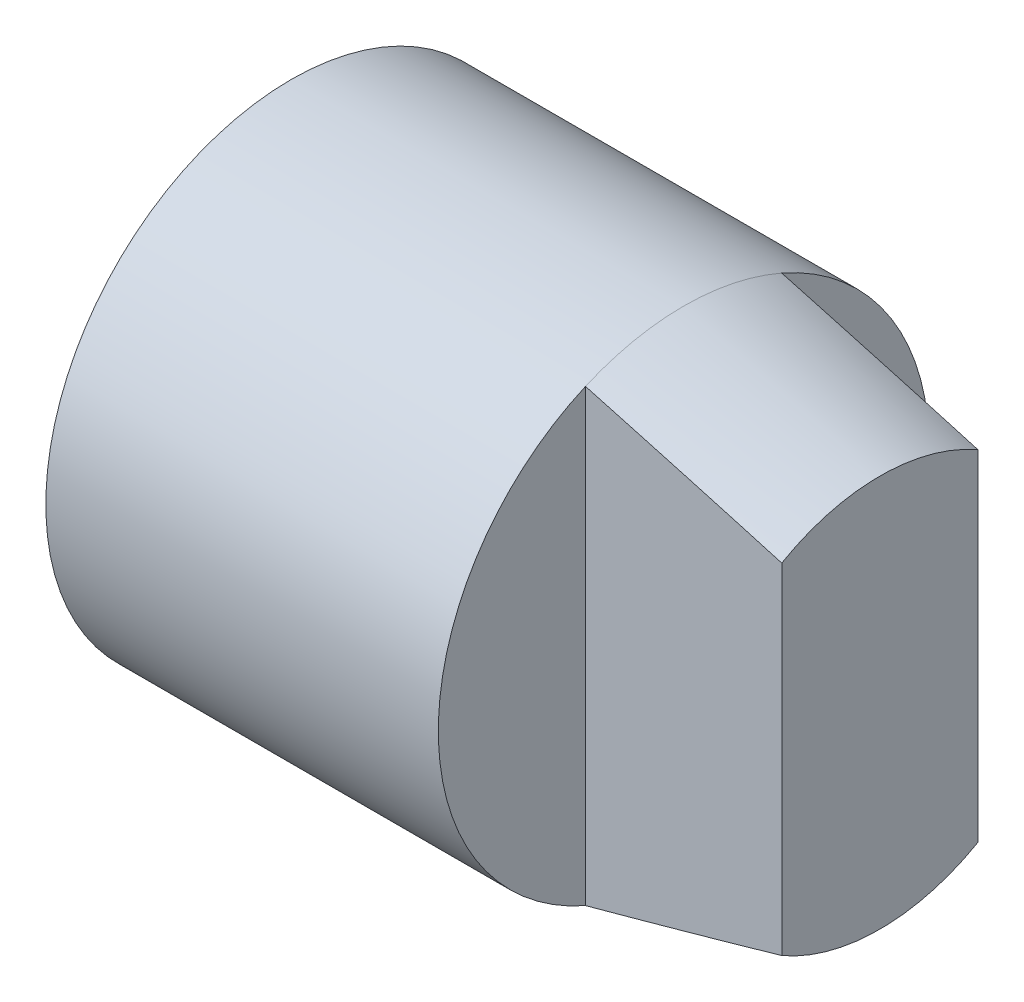
SolidWorks part; units mm, degrees
material "Plain Carbon Steel"
ref_plane "Front Plane" through (0, 0, 0) normal (0, 0, 1) x (1, 0, 0)
ref_plane "Top Plane" through (0, 0, 0) normal (0, 1, 0) x (1, 0, 0)
ref_plane "Right Plane" through (0, 0, 0) normal (1, 0, 0) x (0, 0, -1)
sketch "Sketch1" plane through (0, 0, 0) normal (0, 0, 1) x (1, 0, 0)
  line L0 (0, 0) -> (0, 5)
  line L1 (0, 5) -> (8, 5)
  line L2 (8, 5) -> (12, 4)
  line L3 (12, 4) -> (12, 0)
  line L4 (12, 0) -> (0, 0)
  dimension "D1" = 8
  dimension "D2" = 4
  dimension "D3" = 5
  dimension "D4" = 4
revolve "Revolve1" add sketch "Sketch1" angle 360 about L4
sketch "Sketch2" plane through (12, 0, 0) normal (1, 0, 0) x (0, 0, -1)
  line L0 (-2, 4.5826) -> (-2, -4.5826)
  line L1 (2, -4.5826) -> (2, 4.5826)
  circle A0 centre (0, 0) radius 5 construction
  circle A1 centre (0, 0) radius 5
  circle M4 centre (0, 0) radius 4
  dimension "D1" = 4
extrude "Cut-Extrude1" cut sketch "Sketch2" against normal blind 4 contours L0 M4 | L0 A1 M4 | L1 M4 | L1 A1 M4
